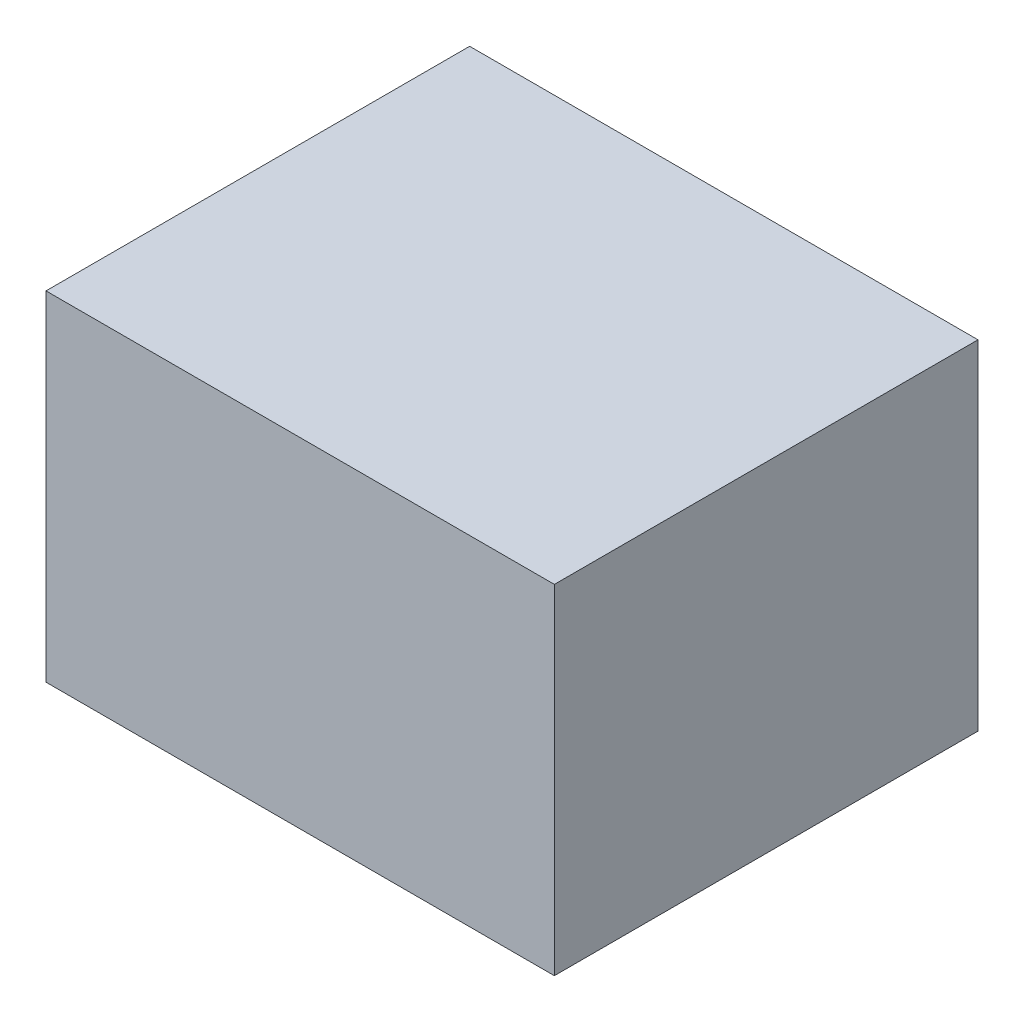
SolidWorks part; units mm, degrees
ref_plane "Front Plane" through (0, 0, 0) normal (0, 0, 1) x (1, 0, 0)
ref_plane "Top Plane" through (0, 0, 0) normal (0, 1, 0) x (1, 0, 0)
ref_plane "Right Plane" through (0, 0, 0) normal (1, 0, 0) x (0, 0, -1)
sketch "Sketch37" plane through (0, 0, 0) normal (0, 0, 1) x (1, 0, 0)
  line L0 (0, 0) -> (0, 15) construction
  line L1 (-10, -20) -> (10, -20)
  line L2 (-10, -20) -> (-10, 20)
  line L3 (-10, 20) -> (10, 20)
  line L4 (10, -20) -> (10, 20)
  line L5 (-10, -20) -> (10, 20) construction
  line L6 (-10, 20) -> (10, -20) construction
  line L7 (-5, -24) -> (5, -24)
  line L8 (-5, -24) -> (-5, 24)
  line L9 (-5, 24) -> (5, 24)
  line L10 (5, -24) -> (5, 24)
  line L11 (-5, -24) -> (5, 24) construction
  line L12 (-5, 24) -> (5, -24) construction
  point P0 (0, 0)
  point P6 (0, 0)
  dimension "D1" = 48
  dimension "D2" = 10
  dimension "D3" = 20
  dimension "D4" = 40
  dimension "D5" = 15
sketch "Sketch40" plane through (0, 0, 0) normal (1, 0, 0) x (0, 0, -1)
  line L0 (-6.35, 6.35) -> (-12.7, 6.35) construction
  line L1 (-6.35, -6.35) -> (6.35, -6.35) construction
  line L2 (-6.35, -6.35) -> (-6.35, 6.35) construction
  line L3 (-6.35, 6.35) -> (6.35, 6.35) construction
  line L4 (6.35, -6.35) -> (6.35, 6.35) construction
  line L5 (-6.35, -6.35) -> (6.35, 6.35) construction
  line L6 (-6.35, 6.35) -> (6.35, -6.35) construction
  line L7 (-15.875, -12.7) -> (15.875, -12.7)
  line L8 (-15.875, -12.7) -> (-15.875, 12.7)
  line L9 (-15.875, 12.7) -> (15.875, 12.7)
  line L10 (15.875, -12.7) -> (15.875, 12.7)
  line L11 (-15.875, -12.7) -> (15.875, 12.7) construction
  line L12 (-15.875, 12.7) -> (15.875, -12.7) construction
  point P0 (0, 0)
  point P6 (0, 0)
  dimension "D1" = 12.7
  dimension "D2" = 25.4
  dimension "D3" = 9.525
  dimension "D4" = 6.35
  dimension "D5" = 3.175
extrude "Boss-Extrude8" add sketch "Sketch40" along normal mid plane 38.1
sketch "Sketch41" plane through (0, 12.7, 0) normal (0, 1, 0) x (1, 0, 0)
  line L0 (19.05, 15.875) -> (-19.05, 15.875) construction
  line L1 (-12.7, 15.875) -> (12.7, 15.875)
  line L2 (-12.7, 15.875) -> (-12.7, -12.7)
  line L3 (-12.7, -12.7) -> (12.7, -12.7)
  line L4 (12.7, 15.875) -> (12.7, -12.7)
  line L5 (-12.7, 15.875) -> (12.7, -12.7) construction
  line L6 (-12.7, -12.7) -> (12.7, 15.875) construction
  point P4 (0, 1.5875)
  point P7 (-13.313, -11.4953)
  point P8 (-10.7537, -11.5824)
  dimension "D1" = 25.4
equation "\"shank_thickness\"= 1"
equation "\"D1@Boss-Extrude8\"=\"shank_thickness\"+.25*2"
equation "\"D1@Sketch41\"=\"shank_thickness\""
